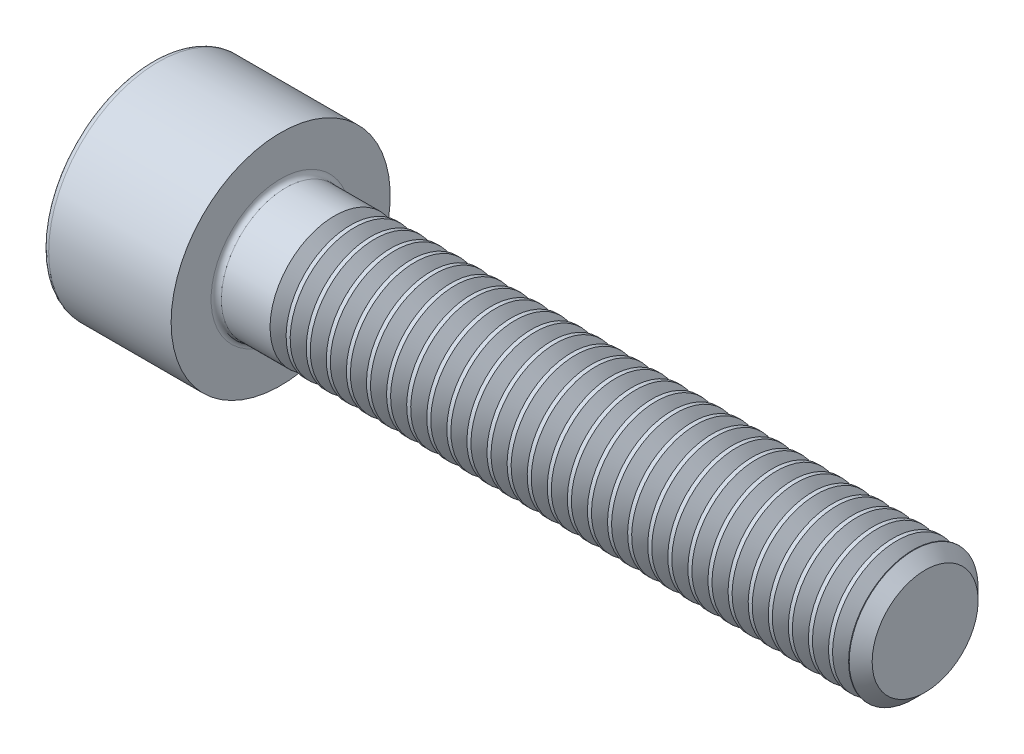
SolidWorks part; units mm, degrees
revolve "Base-Revolve" add sketch "BodySke"
sketch "BodySke" plane through (0, 0, 0) normal (0, 0, 1) x (1, 0, 0)
  line L0 (0, 0) -> (0, 4.25)
  line L1 (0, 4.25) -> (5, 4.25)
  line L2 (5, 4.25) -> (5, 2.5)
  line L3 (5, 2.5) -> (29.555, 2.5)
  line L4 (30, 2.055) -> (30, 0)
  line L5 (30, 0) -> (0, 0)
  line L6 (-31.75, 0) -> (127, 0) construction
  line L8 (30, 2.055) -> (29.555, 2.5)
  line L10 (30, -2.055) -> (29.555, -2.5) construction
  line L11 (5.8, 9.525) -> (5.8, 3.175) construction
  line L12 (5, 9.525) -> (5, 3.175) construction
  line L13 (-30, 9.525) -> (-30, 3.175) construction
  dimension "Head_ht" = 5
  dimension "Length" = 25
  dimension "Body_ch_ang" = 45
  dimension "Diameter" = 5
  dimension "Minor_dia" = 4.11
  dimension "Advance" = 0.8
  dimension "Thread_nom" = 25
  dimension "Thread_length" = 60
  dimension "Head_dia" = 8.5
cosmetic thread "ThreadCosmetic" [suppressed]
fillet "Fillet1" radius 0.2 1 edges at (5, 0, 2.5)
fillet "Fillet2" radius 0.25 1 edges at (0, 0, 4.25)
ref_plane "Plane1" through (0, 0, 0) normal (0, 0, 1) x (1, 0, 0)
ref_plane "Plane2" through (0, 0, 0) normal (0, 1, 0) x (1, 0, 0)
ref_plane "Plane3" through (0, 0, 0) normal (1, 0, 0) x (0, 0, -1)
sketch "Sketch2" plane through (0, 0, 0) normal (0, 0, 1) x (1, 0, 0)
  line L0 (0, 2.042) -> (2.5, 2.042)
  line L1 (2.5, 2.042) -> (3.6789, 0)
  line L2 (-31.75, 0) -> (127, 0) construction
  line L3 (3.6789, 0) -> (0, 0)
  line L4 (0, 0) -> (0, 2.042)
  line L6 (0, 0) -> (47.625, 0) construction
  dimension "D1" = 2.042
  dimension "D2" = 60
  dimension "Depth" = 2.5
revolve "Hex-PreBroach" cut sketch "Sketch2" angle 360 about L6
sketch "Sketch3" plane through (0, 0, 0) normal (-1, 0, 0) x (0, 0.5, 0.866)
  line L0 (1.1789, 2.042) -> (-1.1789, 2.042)
  line L1 (-1.1789, 2.042) -> (-2.3579, 0)
  line L2 (1.1789, 2.042) -> (2.3579, 0)
  line L3 (1.1789, -2.042) -> (2.3579, 0)
  line L4 (1.1789, -2.042) -> (-1.1789, -2.042)
  line L5 (-1.1789, -2.042) -> (-2.3579, 0)
  dimension "D1" = 2.042
  dimension "D2" = 2.042
  dimension "Hex_size" = 4.084
extrude "Hex" cut sketch "Sketch3" against normal blind 2.5
sketch "ThdSchSke" plane through (0, 0, 0) normal (0, 0, 1) x (1, 0, 0)
  line L0 (7.4, -2.055) -> (7.0884, -2.5)
  line L1 (7.4, -2.055) -> (7.7116, -2.5)
  line L2 (7.7116, -2.5) -> (7.7116, -3.125)
  line L3 (-3.175, 0) -> (5.1513, 0) construction
  line L4 (0, 4) -> (0, -4) construction
  line L5 (7.7116, -3.125) -> (7.0884, -3.125)
  line L6 (7.0884, -3.125) -> (7.0884, -2.5)
  dimension "Thread_minor" = 4.11
  dimension "Diameter" = 5
  dimension "Start" = 7.4
revolve "ThreadSchematic" cut sketch "ThdSchSke" angle 360 about L3
pattern_linear "ThdSchPat" count 29 spacing 0.7793 along (1, 0, 0) of "ThreadSchematic"
equation "\"D2@Sketch3\" = \"Hex_size@Sketch3\" / 2"
equation "\"D1@Sketch3\" = \"Hex_size@Sketch3\" / 2"
equation "\"D1@Sketch2\" = \"Hex_size@Sketch3\" / 2"
equation "\"Thread_minor@ThreadCosmetic\"  =  \"Minor_dia@BodySke\""
equation "\"Depth@Sketch2\" =  \"Key_eng@Hex\""
equation "\"Thread_length@ThreadCosmetic\" = ((sgn( (\"Length@BodySke\" - \"Advance@BodySke\" * 3.0) - \"Thread_nom@BodySke\" )-1)*( (\"Length@BodySke\" - \"Advance@BodySke\" * 3.0) - \"Thread_nom@BodySke\" ))/-2+ \"Thread_nom@BodySke\""
equation "\"Thread_minor@ThdSchSke\" = \"Minor_dia@BodySke\""
equation "\"Diameter@ThdSchSke\" = \"Diameter@BodySke\""
equation "\"Overcut@ThdSchSke\" = \"Diameter@BodySke\" * 1.25"
equation "\"Start@ThdSchSke\" = \"Head_ht@BodySke\" + \"Length@BodySke\" - \"Thread_length@ThreadCosmetic\"  '---Non-countersunk---"
equation "\"Num_threads@ThdSchPat\" = int( \"Thread_length@ThreadCosmetic\" / \"Advance@BodySke\" + 0.999 )  + 1"
equation "\"Advance@ThdSchPat\" = \"Thread_length@ThreadCosmetic\" /  (\"Num_threads@ThdSchPat\" - 1) 'relax it"
equation "\"Num_threads@ThdSchPat\" = \"Num_threads@ThdSchPat\" - sgn( \"Num_threads@ThdSchPat\" - 1) '---chamfered tips only---"
